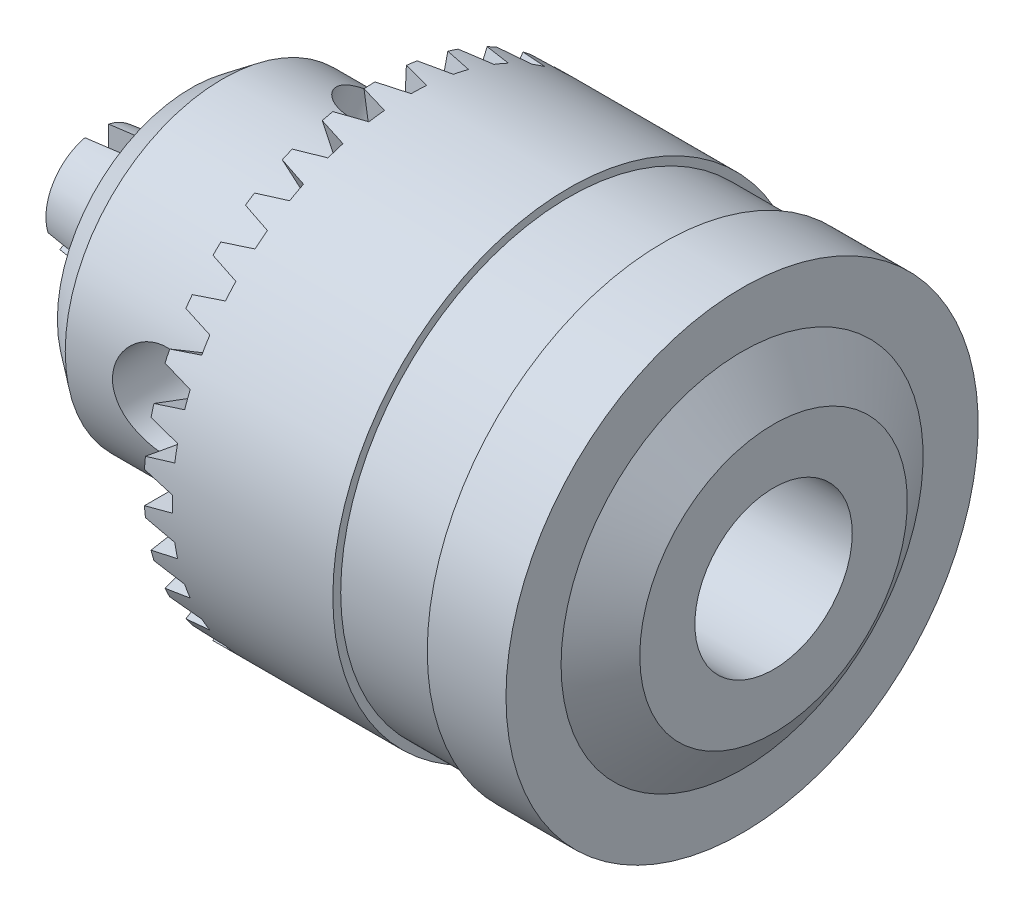
SolidWorks part; units mm, degrees
ref_plane "Ön Düzlem" through (0, 0, 0) normal (0, 0, 1) x (1, 0, 0)
ref_plane "Üst Düzlem" through (0, 0, 0) normal (0, 1, 0) x (1, 0, 0)
ref_plane "Sağ Düzlem" through (0, 0, 0) normal (1, 0, 0) x (0, 0, -1)
sketch "Sketch1" plane through (0, 0, 0) normal (0, 0, 1) x (1, 0, 0)
  line L0 (-18.5, 0) -> (18.5, 0)
  line L1 (18.5, 0) -> (18.5, 8.5)
  line L3 (16.5, 15) -> (11.5, 15)
  line L4 (11.5, 15) -> (11.5, 14.5)
  line L5 (11.5, 14.5) -> (5.5, 14.5)
  line L6 (5.5, 14.5) -> (5.5, 15)
  line L7 (5.5, 15) -> (-6.5, 15)
  line L8 (-6.5, 15) -> (-6.5, 10)
  line L9 (-6.5, 10) -> (-16.5, 10)
  line L10 (-16.5, 10) -> (-18.5, 8.5)
  line L11 (-18.5, 8.5) -> (-18.5, 0)
  line L12 (16.5, 15) -> (16.5, 11.5)
  line L13 (16.5, 11.5) -> (18.5, 8.5)
  dimension "D1" = 15
  dimension "D2" = 14.5
  dimension "D3" = 8.5
  dimension "D4" = 11.5
  dimension "D5" = 2
  dimension "D6" = 5
  dimension "D7" = 8.5
  dimension "D8" = 5
  dimension "D9" = 6
  dimension "D10" = 12
  dimension "D11" = 10
  dimension "D12" = 2
revolve "Revolve1" add sketch "Sketch1" angle 360 about L0
sketch "Sketch2" plane through (18.5, 0, 0) normal (1, 0, 0) x (0, 0, -1)
  circle A0 centre (0, 0) radius 5
  dimension "D1" = 10
extrude "Cut-Extrude1" cut sketch "Sketch2" against normal blind 16.7
sketch "Sketch3" plane through (-18.5, 0, 0) normal (-1, 0, 0) x (0, 0, 1)
  circle A4 centre (0, 0) radius 4
  dimension "D1" = 8
extrude "Cut-Extrude2" cut sketch "Sketch3" against normal up to next
ref_plane "Plane1" through (0, 0, 10) normal (0, 0, 1) x (1, 0, 0)
sketch "Sketch4" plane through (0, 0, 10) normal (0, 0, 1) x (1, 0, 0)
  line L0 (-18.5, 8.5) -> (-18.5, -8.5) construction
  circle A0 centre (-10.5, 0) radius 3
  dimension "D1" = 6
  dimension "D2" = 8
extrude "Cut-Extrude3" cut sketch "Sketch4" against normal blind 4.65
pattern_circular "CirPattern1" count 3 over 360 about axis through (0, 0, 0) along (1, 0, 0) of "Cut-Extrude3"
sketch "Sketch5" plane through (0, 0, 10) normal (0, 0, 1) x (1, 0, 0)
  line L0 (-6.5, 1) -> (-4.7, 0.5)
  line L1 (-6.5, 15) -> (-6.5, -15) construction
  line L2 (-4.7, 0.5) -> (-4.7, -0.5)
  line L3 (-4.7, -0.5) -> (-6.5, -1)
  line L4 (-6.5, -1) -> (-6.5, 1)
  dimension "D1" = 1.8
  dimension "D2" = 1
  dimension "D3" = 2
  dimension "D4" = 1
  dimension "D5" = 0.5
extrude "Cut-Extrude4" cut sketch "Sketch5" along normal up to next (5 mm away)
pattern_circular "CirPattern2" count 35 over 360 about axis through (0, 0, 0) along (1, 0, 0) of "Cut-Extrude4"
sketch "Sketch6" plane through (-18.5, 0, 0) normal (-1, 0, 0) x (0, 0, 1)
  line L3 (0.75, 3.9774) -> (0.75, 0.433)
  line L4 (0.75, 0.433) -> (3.8195, -1.3392)
  line L5 (-0.75, 3.9774) -> (-0.75, 0.433)
  line L6 (-0.75, 0.433) -> (-3.8195, -1.3392)
  line L7 (-5.1354, 0) -> (-1.5, 0) construction
  line L8 (0, -0.866) -> (-3.0695, -2.6382)
  line L9 (0, -0.866) -> (3.0695, -2.6382)
  line L10 (1.5, 0) -> (6.6582, 0) construction
  arc A1 (-0.75, 3.9774) -> (-3.8195, -1.3392) centre (0, 0) ccw
  arc A2 (3.8195, -1.3392) -> (0.75, 3.9774) centre (0, 0) ccw
  arc A3 (-3.0695, -2.6382) -> (3.0695, -2.6382) centre (0, 0) ccw
extrude "Boss-Extrude1" add sketch "Sketch6" along normal blind 6
ref_plane "Plane2" through (0, 0, 0) normal (0, 0.866, -0.5) x (1, 0, 0)
sketch "Sketch12" plane through (0, 0, 0) normal (0, 0.866, -0.5) x (1, 0, 0)
  line L0 (-18.5, 4.3774) -> (-24.5, 4.3774)
  line L1 (-18.5, 8.5) -> (-18.5, -8.5) construction
  line L2 (-24.5, 4.3774) -> (-24.5, 3.2274)
  line L3 (-24.5, 3.9774) -> (-24.5, -1.3392) construction
  line L5 (-24.5, 3.2274) -> (-18.5, 3.9774)
  line L6 (-18.5, 3.9774) -> (-18.5, -1.3392) construction
  line L7 (-18.5, 3.9774) -> (-18.5, 4.3774)
  line L8 (-10.3744, 0) -> (-28.5701, 0) construction
  dimension "D1" = 0.75
  dimension "D2" = 0.4
revolve "Cut-Revolve3" cut sketch "Sketch12" angle 360 about L8
sketch "Sketch14" plane through (0, 0, 0) normal (0, 0.866, -0.5) x (1, 0, 0)
  line L0 (-18.5, 0.433) -> (-13.4547, 4)
  line L1 (1.8, 4) -> (-18.5, 4) construction
  line L2 (-18.5, 0.433) -> (-18.5, 4)
  line L3 (-18.5, 4) -> (-13.4547, 4)
  line L4 (-10.5, 0) -> (-27.1183, 0) construction
revolve "Revolve2" add sketch "Sketch14" angle 360 about L4
sketch "Sketch15" plane through (-18.5, 0, 0) normal (-1, 0, 0) x (0, 0, 1)
  line L0 (0.75, 3.906) -> (0.75, 0.433) construction
  line L1 (0.75, 0.433) -> (3.7577, -1.3035) construction
  line L2 (3.0077, -2.6025) -> (0, -0.866) construction
  line L3 (0, -0.866) -> (-3.0077, -2.6025) construction
  line L4 (-3.7577, -1.3035) -> (-0.75, 0.433) construction
  line L5 (-0.75, 0.433) -> (-0.75, 3.906) construction
  line L6 (0.75, 3.906) -> (0.75, 0.433)
  line L7 (0.75, 0.433) -> (3.7577, -1.3035)
  line L8 (3.0077, -2.6025) -> (0, -0.866)
  line L9 (0, -0.866) -> (-3.0077, -2.6025)
  line L10 (-3.7577, -1.3035) -> (-0.75, 0.433)
  line L11 (-0.75, 0.433) -> (-0.75, 3.906)
  line L12 (-0.75, 3.906) -> (0.75, 3.906)
  line L13 (3.7577, -1.3035) -> (3.0077, -2.6025)
  line L14 (-3.7577, -1.3035) -> (-3.0077, -2.6025)
extrude "Cut-Extrude5" cut sketch "Sketch15" against normal up to next
scale "Scale1" scale about centroid uniform scaling yes scale factor 2.5
